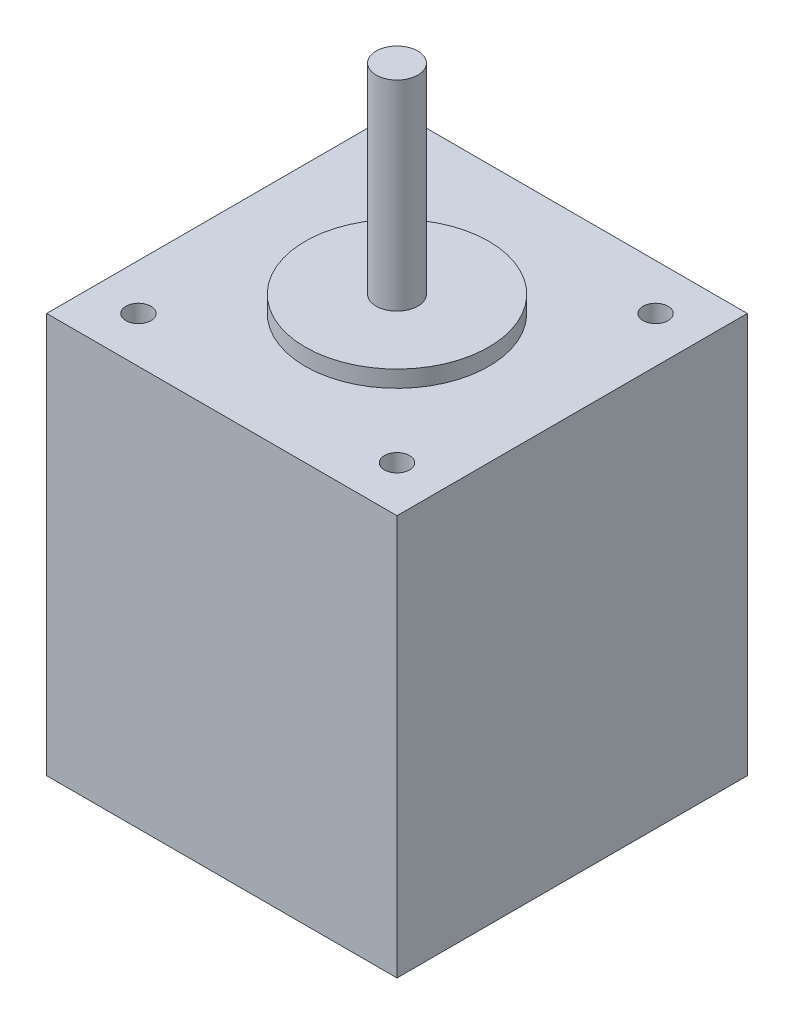
SolidWorks part; units mm, degrees
ref_plane "Front Plane" through (0, 0, 0) normal (0, 0, 1) x (1, 0, 0)
ref_plane "Top Plane" through (0, 0, 0) normal (0, 1, 0) x (1, 0, 0)
ref_plane "Right Plane" through (0, 0, 0) normal (1, 0, 0) x (0, 0, -1)
sketch "Sketch1" plane through (0, 0, 0) normal (0, 1, 0) x (1, 0, 0)
  line L1 (0, 0) -> (42, 0)
  line L2 (0, 0) -> (0, 42)
  line L3 (0, 42) -> (42, 42)
  line L4 (42, 0) -> (42, 42)
  line L5 (0, 0) -> (42, 42) construction
  line L6 (0, 42) -> (42, 0) construction
  point P4 (21, 21)
  dimension "D1" = 42
  dimension "D2" = 42
extrude "Boss-Extrude1" add sketch "Sketch1" along normal blind 48
sketch "Sketch5" plane through (0, 48, 0) normal (0, 1, 0) x (1, 0, 0)
  line L0 (42, 21) -> (0, 21) construction
  line L1 (42, 0) -> (42, 42) construction
  line L2 (0, 42) -> (0, 0) construction
  line L3 (21, 0) -> (21, 42) construction
  line L4 (0, 0) -> (42, 0) construction
  line L5 (42, 42) -> (0, 42) construction
  circle A0 centre (21, 21) radius 11
  dimension "D1" = 22
extrude "Boss-Extrude4" add sketch "Sketch5" along normal blind 2
sketch "Sketch6" plane through (0, 50, 0) normal (0, 1, 0) x (1, 0, 0)
  circle A0 centre (21, 21) radius 2.5
  dimension "D1" = 5
extrude "Boss-Extrude5" add sketch "Sketch6" along normal blind 24
sketch "Sketch8" plane through (0, 48, 0) normal (0, 1, 0) x (1, 0, 0)
  line L0 (36.5, 42) -> (36.5, 0) construction
  line L1 (42, 42) -> (0, 42) construction
  line L2 (0, 0) -> (42, 0) construction
  line L3 (42, 5.5) -> (0, 5.5) construction
  line L4 (42, 0) -> (42, 42) construction
  line L5 (0, 42) -> (0, 0) construction
  line L6 (42, 21) -> (0, 21) construction
  line L7 (21, 42) -> (21, 0) construction
  circle A0 centre (36.5, 5.5) radius 1.5
  circle A1 centre (36.5, 36.5) radius 1.5
  circle A2 centre (5.5, 5.5) radius 1.5
  circle A3 centre (5.5, 36.5) radius 1.5
  dimension "D3" = 3
  dimension "D1" = 15.5
  dimension "D2" = 15.5
extrude "Cut-Extrude1" cut sketch "Sketch8" against normal blind 4.5
